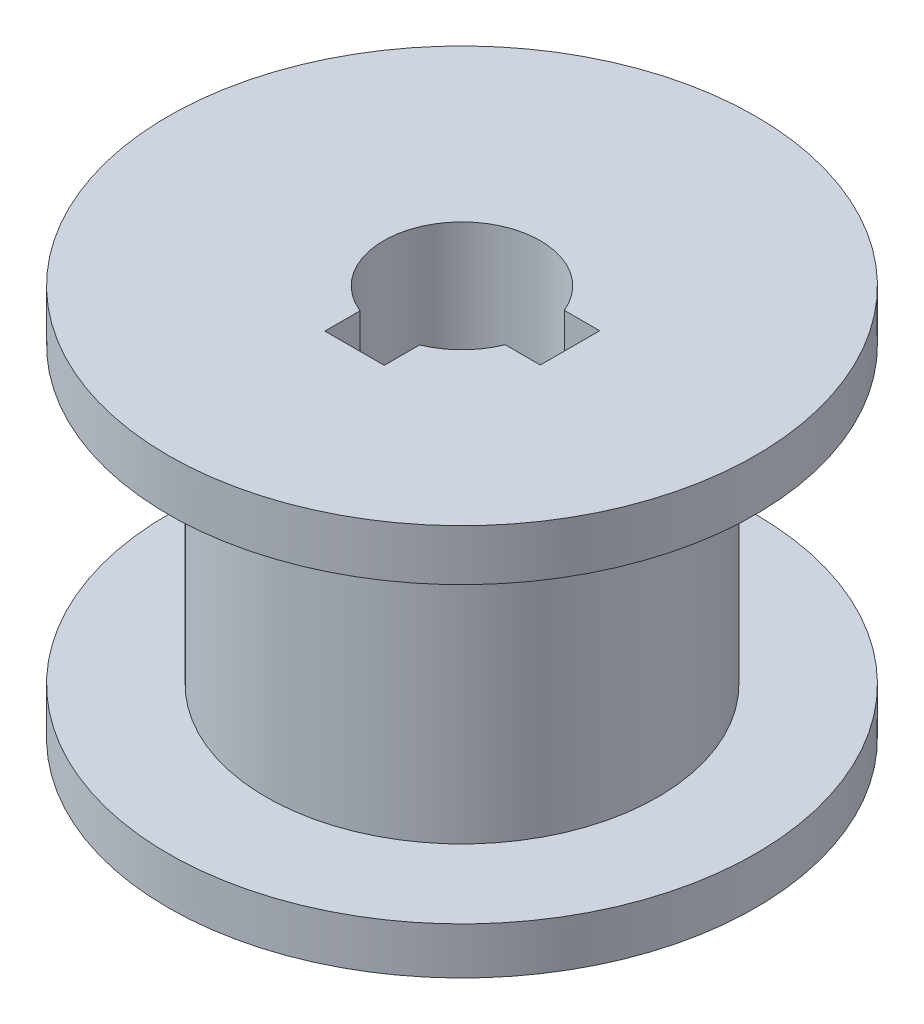
SolidWorks part; units mm, degrees
material "1060 合金"
ref_plane "前视基准面" through (0, 0, 0) normal (0, 0, 1) x (1, 0, 0)
ref_plane "上视基准面" through (0, 0, 0) normal (0, 1, 0) x (1, 0, 0)
ref_plane "右视基准面" through (0, 0, 0) normal (1, 0, 0) x (0, 0, -1)
sketch "草图1" plane through (0, 0, 0) normal (0, 1, 0) x (1, 0, 0)
  line L0 (0, -5.5) -> (-1.5, -5.5)
  line L1 (5.5, 0) -> (5.5, -1.5)
  line L2 (5.5, -1.5) -> (3.7081, -1.5)
  line L3 (5.5, 0) -> (5.5, 1.53)
  line L4 (5.5, 1.53) -> (3.6958, 1.53)
  line L5 (-1.5, -5.5) -> (-1.5, -3.7081)
  line L6 (0, -5.5) -> (1.53, -5.5)
  line L7 (1.53, -5.5) -> (1.53, -3.6958)
  circle A0 centre (0, 0) radius 4
  circle A1 centre (0, 0) radius 15
  point P17 (0, 0)
  dimension "D1" = 2
extrude "凸台-拉伸1" add sketch "草图1" along normal blind 20 contours A1 A0 L7 L6 L0 L5 L4 L3 L1 L2
sketch "草图2" plane through (0, 0, 0) normal (0, 0, 1) x (1, 0, 0)
  line L0 (0, 0) -> (0, 20)
  line L2 (15, 17.392) -> (10, 17.392)
  line L3 (15, 17.392) -> (15, 2.392)
  line L5 (10, 17.392) -> (10, 2.392)
  line L6 (10, 2.392) -> (15, 2.392)
revolve "切除-旋转1" cut sketch "草图2" angle 360 about L0
ref_plane "基准面1" through (0, 10, 0) normal (0, 1, 0) x (1, 0, 0)
sketch "草图3" plane through (0, 0, 0) normal (0, -1, 0) x (1, 0, 0)
  line L12 (5.5, 1.5) -> (3.7081, 1.5)
  line L13 (5.5, -1.53) -> (5.5, 1.5)
  line L14 (3.6958, -1.53) -> (5.5, -1.53)
  line L15 (-1.5, 5.5) -> (-1.5, 3.7081)
  line L16 (1.53, 5.5) -> (-1.5, 5.5)
  line L17 (1.53, 3.6958) -> (1.53, 5.5)
  line L18 (5.5, 1.5) -> (3.7081, 1.5)
  line L19 (5.5, -1.53) -> (5.5, 1.5)
  line L20 (3.6958, -1.53) -> (5.5, -1.53)
  line L21 (-1.5, 5.5) -> (-1.5, 3.7081)
  line L22 (1.53, 5.5) -> (-1.5, 5.5)
  line L23 (1.53, 3.6958) -> (1.53, 5.5)
  circle A1 centre (0, 0) radius 15
  circle A2 centre (0, 0) radius 15
  arc A6 (3.7081, 1.5) -> (1.53, 3.6958) centre (0, 0) ccw
  arc A7 (-1.5, 3.7081) -> (3.6958, -1.53) centre (0, 0) ccw
  arc A8 (3.7081, 1.5) -> (1.53, 3.6958) centre (0, 0) ccw
  arc A9 (-1.5, 3.7081) -> (3.6958, -1.53) centre (0, 0) ccw
  dimension "D1" = 0
  dimension "D2" = 0
